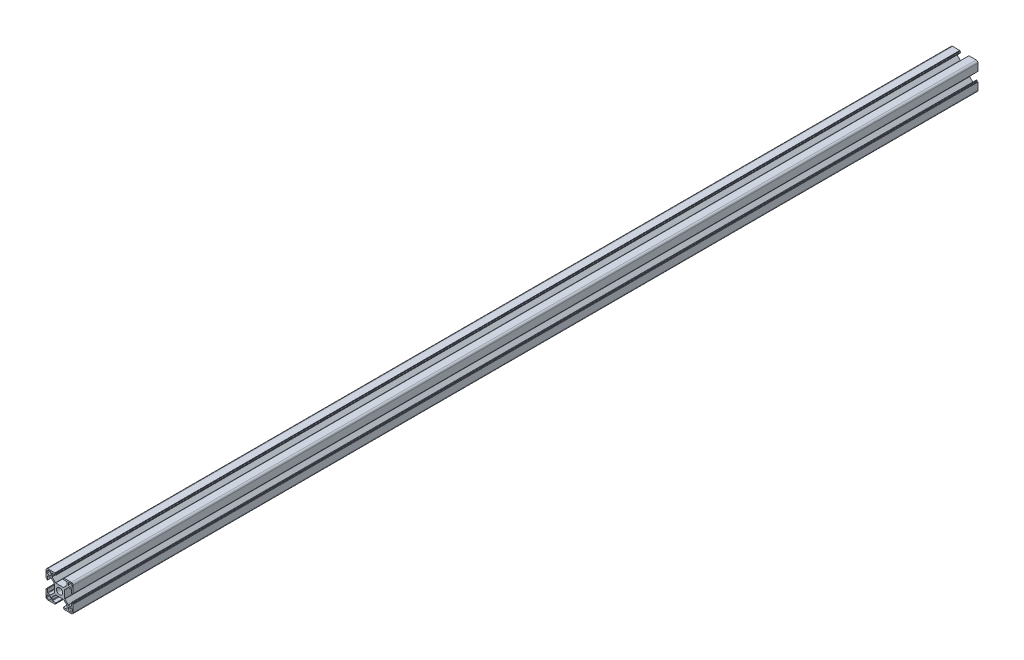
SolidWorks part; units mm, degrees
ref_plane "前视基准面" through (0, 0, 0) normal (0, 0, 1) x (1, 0, 0)
ref_plane "上视基准面" through (0, 0, 0) normal (0, 1, 0) x (1, 0, 0)
ref_plane "右视基准面" through (0, 0, 0) normal (1, 0, 0) x (0, 0, -1)
sketch "草图1" plane through (0, 0, 0) normal (0, 0, 1) x (1, 0, 0)
  line L0 (0, 0) -> (0, 65.3905) construction
  line L1 (0, 0) -> (64.2648, 0) construction
  line L2 (0, 0) -> (79.9729, 79.9729) construction
  line L3 (5.7, 0) -> (5.7, 4.4272)
  line L4 (5.7, 4.4272) -> (9.6728, 8.4)
  line L5 (9.6728, 8.4) -> (13.2, 8.4)
  line L6 (13.2, 8.4) -> (13.2, 4.1)
  line L7 (13.2, 4.1) -> (14.1, 4.1)
  line L8 (14.1, 4.1) -> (14.1, 5.1)
  line L9 (14.1, 5.1) -> (15, 5.1)
  line L10 (15, 5.1) -> (15, 15)
  line L11 (5.1, 15) -> (15, 15)
  line L12 (5.1, 14.1) -> (5.1, 15)
  line L13 (4.1, 14.1) -> (5.1, 14.1)
  line L14 (4.1, 13.2) -> (4.1, 14.1)
  line L15 (8.4, 13.2) -> (4.1, 13.2)
  line L16 (8.4, 9.6728) -> (8.4, 13.2)
  line L17 (4.4272, 5.7) -> (8.4, 9.6728)
  line L18 (0, 5.7) -> (4.4272, 5.7)
  line L20 (9.7, 9.7) -> (13.7, 9.7)
  line L21 (9.7, 9.7) -> (9.7, 13.7)
  line L22 (9.7, 13.7) -> (13.7, 13.7)
  line L23 (13.7, 9.7) -> (13.7, 13.7)
  line L24 (9.7, 9.7) -> (13.7, 13.7) construction
  line L25 (9.7, 13.7) -> (13.7, 9.7) construction
  line L26 (0, 5.7) -> (0, 0)
  line L27 (0, 0) -> (5.7, 0)
  point P9 (11.7, 11.7)
  dimension "D1" = 45
  dimension "D2" = 5.7
  dimension "D3" = 1.8
  dimension "D4" = 0.9
  dimension "D5" = 8.2
  dimension "D6" = 10.2
  dimension "D7" = 1.8
  dimension "D8" = 15
  dimension "D9" = 16.8
  dimension "D10" = 4
  dimension "D11" = 1.3
extrude "凸台-拉伸1" add sketch "草图1" along normal blind 1000 contours L3 L4 L5 L6 L7 L8 L9 L10 L11 L12 L13 L14 L15 L16 L17 L18 L26 L27
fillet "圆角1" radius 1 4 edges at (9.7, 9.7, 500) (13.7, 9.7, 500) (9.7, 13.7, 500) (13.7, 13.7, 500)
fillet "圆角2" radius 2 1 edges at (15, 15, 500)
fillet "圆角3" radius 0.5 6 edges at (5.7, 4.4272, 500) (4.4272, 5.7, 500) (8.4, 13.2, 500) (8.4, 9.6728, 500) (9.6728, 8.4, 500) (13.2, 8.4, 500)
pattern_circular "阵列(圆周)1" count 4 over 360 about axis through (0, 0, 0) along (0, 0, 1) of "圆角2", "圆角3", "凸台-拉伸1", "圆角1"
sketch "草图2" plane through (0, 0, 1000) normal (0, 0, 1) x (1, 0, 0)
  circle A0 centre (0, 0) radius 3.4
  dimension "D1" = 6.8
extrude "切除-拉伸1" cut sketch "草图2" against normal through all
sketch "草图3" plane through (0, 0, 0) normal (0, 1, 0) x (1, 0, 0)
  line L0 (-124.529, -500) -> (298.0898, -500) construction
  line L3 (4.2201, -1000) -> (-4.2201, -1000) construction
  line L4 (4.2201, 0) -> (-4.2201, 0) construction
  line L5 (0, 75.7926) -> (0, -1090.9772) construction
  line L6 (-4, -70) -> (-4, -80)
  line L7 (4, -80) -> (4, -70)
  line L8 (4, -920) -> (4, -930)
  line L9 (-4, -930) -> (-4, -920)
  circle A0 centre (0, -20) radius 4
  circle A1 centre (0, -980) radius 4
  arc A2 (4, -70) -> (-4, -70) centre (0, -70) ccw
  arc A3 (-4, -80) -> (4, -80) centre (0, -80) ccw
  arc A4 (-4, -920) -> (4, -920) centre (0, -920) cw
  arc A5 (4, -930) -> (-4, -930) centre (0, -930) cw
  dimension "D1" = 8
  dimension "D2" = 480
  dimension "D3" = 8
  dimension "D4" = 50
  dimension "D5" = 8
  dimension "D6" = 10
extrude "切除-拉伸2" cut sketch "草图3" against normal mid plane 20
sketch "草图4" plane through (0, 0, 0) normal (1, 0, 0) x (0, 0, -1)
  line L0 (-500, 183.6723) -> (-500, -167.1159) construction
  line L1 (-1120.864, 0) -> (144.6637, 0) construction
  line L2 (0, 5.1) -> (0, 13) construction
  line L3 (-1000, 5.1) -> (-1000, 13) construction
  circle A0 centre (-945, 0) radius 3.1
  circle A1 centre (-915, 0) radius 3.1
  circle A2 centre (-85, 0) radius 3.1
  circle A3 centre (-55, 0) radius 3.1
  circle A4 centre (-500, 0) radius 4.1
  dimension "D1" = 6.2
  dimension "D2" = 30
  dimension "D3" = 445
  dimension "D4" = 8.2
extrude "切除-拉伸3" cut sketch "草图4" against normal mid plane 15
